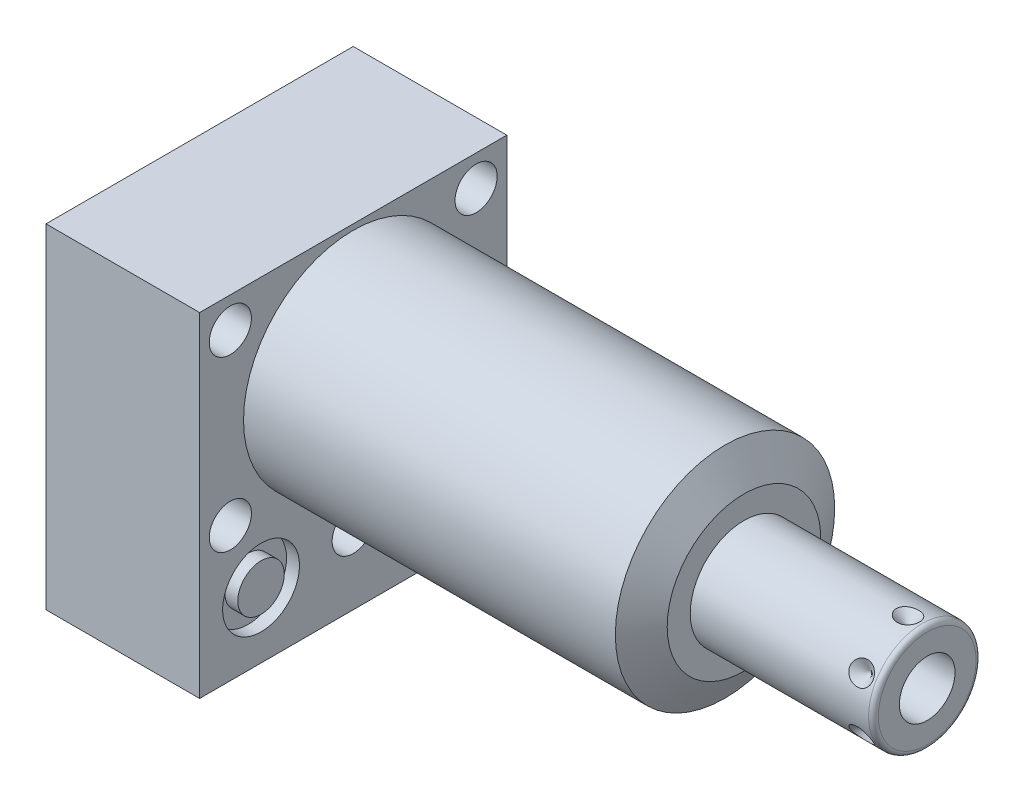
SolidWorks part; units mm, degrees
material "Alloy Steel"
ref_plane "Front Plane" through (0, 0, 0) normal (0, 0, 1) x (1, 0, 0)
ref_plane "Top Plane" through (0, 0, 0) normal (0, 1, 0) x (1, 0, 0)
ref_plane "Right Plane" through (0, 0, 0) normal (1, 0, 0) x (0, 0, -1)
ref_plane "Plane1" through (0, 0, 0) normal (1, 0, 0) x (0, 0, -1)
sketch "Sketch1" plane through (0, 0, 0) normal (1, 0, 0) x (0, 0, -1)
  line L0 (-31.75, 23.8252) -> (-31.75, -45.2628)
  line L1 (-31.75, -45.2628) -> (31.75, -45.2628)
  line L2 (31.75, -45.2628) -> (31.75, 23.8252)
  line L3 (31.75, 23.8252) -> (-31.75, 23.8252)
  line L4 (0, -55.6514) -> (0, 27.6098) construction
  dimension "D1" = 63.5
  dimension "D2" = 69.088
  dimension "D3" = 23.8252
extrude "Extrude1" add sketch "Sketch1" along normal blind 80.772 and the other way blind 31.75
ref_plane "Plane2" through (0, 0, 0) normal (1, 0, 0) x (0, 0, -1)
sketch "Sketch2" plane through (0, 0, 0) normal (1, 0, 0) x (0, 0, -1)
  line L0 (-26.0541, 0) -> (26.0541, 0) construction
  line L5 (31.75, 23.8252) -> (-31.75, 23.8252)
  line L6 (-31.75, 23.8252) -> (-31.75, -45.2628)
  line L7 (-31.75, -45.2628) -> (31.75, -45.2628)
  line L8 (31.75, -45.2628) -> (31.75, 23.8252)
  line L9 (31.75, 23.8252) -> (-31.75, 23.8252)
  line L10 (-31.75, 23.8252) -> (-31.75, -45.2628)
  line L11 (-31.75, -45.2628) -> (31.75, -45.2628)
  line L12 (31.75, -45.2628) -> (31.75, 23.8252)
  circle A0 centre (0, 0) radius 22.6695
  dimension "D1" = 45.339
  dimension "D2" = 0
extrude "Cut-Extrude1" cut sketch "Sketch2" along normal up to next
ref_plane "Plane3" through (0, 0, 0) normal (0, 0, 1) x (1, 0, 0)
sketch "Sketch3" plane through (0, 0, 0) normal (0, 0, 1) x (1, 0, 0)
  line L0 (76.8492, 22.6695) -> (80.772, 15.875)
  line L1 (76.0371, 0) -> (80.9975, 0) construction
  line L2 (80.772, 22.6695) -> (80.772, 15.875)
  line L3 (80.772, 22.6695) -> (76.8492, 22.6695)
  line L4 (80.772, 22.6695) -> (0, 22.6695) construction
  line L5 (80.772, -22.6695) -> (80.772, 22.6695) construction
  dimension "D1" = 31.75
  dimension "D2" = 30
revolve "Cut-Revolve1" cut sketch "Sketch3" angle 360 about L1
ref_plane "Plane4" through (-29.083, -31.75, 19.05) normal (0, 0, 1) x (0, 1, 0)
sketch "S2D0002" plane through (-29.083, -31.75, 19.05) normal (0, 0, 1) x (0, 1, 0)
  line L0 (0, 0) -> (4.5466, 0)
  line L1 (4.5466, 0) -> (4.1066, -2.0701)
  line L2 (4.1066, -2.0701) -> (3.4544, -2.7223)
  line L3 (3.4544, -2.7223) -> (3.4544, -13.97)
  line L4 (3.4544, -13.97) -> (0, -13.97)
  line L5 (0, -13.97) -> (0, 0)
  line L6 (0, -14.6685) -> (0, 0.6985) construction
  dimension "D1" = 13.97
revolve "Cut-Revolve2" cut sketch "S2D0002" angle 360 about L6
ref_plane "Plane5" through (-29.083, -31.75, -19.05) normal (0, 0, 1) x (0, 1, 0)
sketch "Sketch5" plane through (-29.083, -31.75, -19.05) normal (0, 0, 1) x (0, 1, 0)
  line L0 (0, 0) -> (4.5466, 0)
  line L1 (4.5466, 0) -> (4.1066, -2.0701)
  line L2 (4.1066, -2.0701) -> (3.4544, -2.7223)
  line L3 (3.4544, -2.7223) -> (3.4544, -13.97)
  line L4 (3.4544, -13.97) -> (0, -13.97)
  line L5 (0, -13.97) -> (0, 0)
  line L6 (0, -14.6685) -> (0, 0.6985) construction
  dimension "D1" = 13.97
revolve "Cut-Revolve3" cut sketch "Sketch5" angle 360 about L6
ref_plane "Plane6" through (-2.667, -31.75, 19.05) normal (0, 0, 1) x (0, -1, 0)
sketch "Sketch6" plane through (-2.667, -31.75, 19.05) normal (0, 0, 1) x (0, -1, 0)
  line L0 (0, 0) -> (4.5466, 0)
  line L1 (4.5466, 0) -> (4.1066, -2.0701)
  line L2 (4.1066, -2.0701) -> (3.4544, -2.7223)
  line L3 (3.4544, -2.7223) -> (3.4544, -12.192)
  line L4 (3.4544, -12.192) -> (0, -12.192)
  line L5 (0, -12.192) -> (0, 0)
  line L6 (0, -12.8016) -> (0, 0.6096) construction
  dimension "D1" = 12.192
revolve "Cut-Revolve4" cut sketch "Sketch6" angle 360 about L6
ref_plane "Plane7" through (-2.667, -31.75, -19.05) normal (0, 0, 1) x (0, -1, 0)
sketch "Sketch7" plane through (-2.667, -31.75, -19.05) normal (0, 0, 1) x (0, -1, 0)
  line L0 (0, 0) -> (4.5466, 0)
  line L1 (4.5466, 0) -> (4.1066, -2.0701)
  line L2 (4.1066, -2.0701) -> (3.4544, -2.7223)
  line L3 (3.4544, -2.7223) -> (3.4544, -12.192)
  line L4 (3.4544, -12.192) -> (0, -12.192)
  line L5 (0, -12.192) -> (0, 0)
  line L6 (0, -12.8016) -> (0, 0.6096) construction
  dimension "D1" = 12.192
revolve "Cut-Revolve5" cut sketch "Sketch7" angle 360 about L6
ref_plane "Plane8" through (-15.875, -51.6128, 19.05) normal (0, 0, 1) x (-1, 0, 0)
sketch "Sketch8" plane through (-15.875, -51.6128, 19.05) normal (0, 0, 1) x (-1, 0, 0)
  line L0 (0, -6.604) -> (6.1849, -6.604)
  line L1 (6.1849, -6.604) -> (5.6423, -9.1567)
  line L2 (5.6423, -9.1567) -> (4.9784, -9.8206)
  line L3 (4.9784, -9.8206) -> (4.9784, -25.654)
  line L4 (4.9784, -25.654) -> (0, -25.654)
  line L5 (0, -25.654) -> (0, -6.604)
  line L6 (0, -26.67) -> (0, 1.27) construction
  line L8 (15.875, -6.35) -> (-15.875, -6.35) construction
  dimension "D1" = 19.05
  dimension "D2" = 0.254
revolve "Cut-Revolve6" cut sketch "Sketch8" angle 360 about L6
ref_plane "Plane9" through (-15.875, -51.6128, -19.05) normal (0, 0, 1) x (-1, 0, 0)
sketch "Sketch9" plane through (-15.875, -51.6128, -19.05) normal (0, 0, 1) x (-1, 0, 0)
  line L0 (0, -6.604) -> (6.1849, -6.604)
  line L1 (6.1849, -6.604) -> (5.6423, -9.1567)
  line L2 (5.6423, -9.1567) -> (4.9784, -9.8206)
  line L3 (4.9784, -9.8206) -> (4.9784, -25.654)
  line L4 (4.9784, -25.654) -> (0, -25.654)
  line L5 (0, -25.654) -> (0, -6.604)
  line L6 (0, -26.67) -> (0, 1.27) construction
  line L7 (15.875, -6.35) -> (-15.875, -6.35) construction
  dimension "D1" = 19.05
  dimension "D2" = 0.254
revolve "Cut-Revolve7" cut sketch "Sketch9" angle 360 about L6
ref_plane "Plane10" through (0, 0, 0) normal (0, 0, 1) x (1, 0, 0)
sketch "Sketch18" plane through (0, 0, 0) normal (1, 0, 0) x (0, 0, -1)
  circle A0 centre (-19.05, -31.75) radius 7.9375
  circle A1 centre (19.05, -31.75) radius 7.9375
  dimension "D1" = 15.875
extrude "Cut-Extrude2" cut sketch "Sketch18" against normal blind 2.667
sketch "Sketch19" plane through (-31.75, 0, 0) normal (-1, 0, 0) x (0, 0, 1)
  circle A0 centre (-19.05, -31.75) radius 7.9375
  circle A1 centre (19.05, -31.75) radius 7.9375
  dimension "D1" = 15.875
extrude "Cut-Extrude3" cut sketch "Sketch19" against normal blind 2.667
sketch "Sketch20" plane through (0, -45.2628, 0) normal (0, -1, 0) x (1, 0, 0)
  circle A0 centre (-15.875, -19.05) radius 9.525
  circle A1 centre (-15.875, 19.05) radius 9.525
  circle A2 centre (-15.875, 19.05) radius 6.1849 construction
  dimension "D1" = 19.05
extrude "Cut-Extrude4" cut sketch "Sketch20" against normal blind 0.254
sketch "Sketch10" plane through (0, 0, 0) normal (0, 0, 1) x (1, 0, 0)
  line L0 (80.772, 0) -> (80.772, 11.1125)
  line L1 (80.772, 11.1125) -> (117.6274, 11.1125)
  line L2 (118.6434, 10.0965) -> (118.6434, 0)
  line L3 (118.6434, 0) -> (80.772, 0)
  line L4 (58.2708, 0) -> (120.537, 0) construction
  line L5 (80.772, -15.875) -> (80.772, 15.875) construction
  line L6 (-31.75, 23.8252) -> (-31.75, -45.2628) construction
  arc A0 (118.6434, 10.0965) -> (117.6274, 11.1125) centre (117.6274, 10.0965) ccw
  point P0 (80.772, 0)
  dimension "D2" = 1.016
  dimension "D1" = 22.225
  dimension "D3" = 150.3934
revolve "Revolve1" add sketch "Sketch10" angle 360 about L4
ref_plane "Plane11" through (118.6434, -5.7531, 0) normal (0, 0, 1) x (0, -1, 0)
sketch "S2D0001" plane through (118.6434, -5.7531, 0) normal (0, 0, 1) x (0, -1, 0)
  line L0 (0, 0) -> (0, -17.018)
  line L1 (0, -17.018) -> (-5.7531, -20.4748)
  line L2 (0, 0) -> (-5.7531, 0)
  line L3 (-5.7531, 0) -> (-5.7531, -20.4748)
  line L4 (-5.7531, -34.3471) -> (-5.7531, 1.0237) construction
  line L5 (4.3434, 0) -> (-15.8496, 0) construction
  dimension "D1" = 11.5062
  dimension "D2" = 17.018
  dimension "D3" = 59
revolve "Cut-Revolve8" cut sketch "S2D0001" angle 360 about L4
ref_plane "Plane12" through (-31.75, -51.6128, 0) normal (0, -1, 0) x (0, 0, -1)
sketch "Sketch12" plane through (0, -45.0088, 0) normal (0, -1, 0) x (1, 0, 0)
  circle A0 centre (-15.875, 19.05) radius 6.4389
  circle A1 centre (-15.875, 19.05) radius 9.525 construction
  dimension "D1" = 12.8778
extrude "Extrude2" add sketch "Sketch12" along normal blind 1.651
sketch "Sketch13" plane through (0, 0, 0) normal (1, 0, 0) x (0, 0, -1)
  circle A0 centre (-19.05, -31.75) radius 4.8006
  circle A1 centre (-19.05, -31.75) radius 7.9375 construction
  dimension "D1" = 9.6012
ref_plane "Plane13" through (-31.75, 0, 0) normal (1, 0, 0) x (0, 0, -1)
extrude "Extrude3" add sketch "Sketch13" along normal up to surface
ref_plane "Plane14" through (0, -31.75, -19.05) normal (0, -1, 0) x (0, 0, -1)
sketch "Sketch14" plane through (0, -31.75, -19.05) normal (0, -1, 0) x (0, 0, -1)
  line L0 (0, -2.8435) -> (0, 1.0401) construction
  line L1 (0, -5.3893) -> (0, -12.2901) construction
  line L2 (7.9375, -2.667) -> (-7.9375, -2.667) construction
  circle A0 centre (6.1722, -0.9017) radius 1.7653
  dimension "D1" = 3.5306
  dimension "D2" = 12.3444
revolve "Revolve2" add sketch "Sketch14" angle 360 about L0
ref_plane "Plane15" through (0, -31.75, -19.05) normal (0, -1, 0) x (0, 0, -1)
sketch "Sketch15" plane through (0, -31.75, -19.05) normal (0, -1, 0) x (0, 0, -1)
  line L0 (0, -32.7901) -> (0, -28.9065) construction
  line L1 (0, -29.083) -> (0, -27.0129) construction
  line L2 (-7.9375, -29.083) -> (7.9375, -29.083) construction
  circle A0 centre (6.1722, -30.8483) radius 1.7653
  dimension "D1" = 3.5306
  dimension "D2" = 12.3444
revolve "Revolve3" add sketch "Sketch15" angle 360 about L0
ref_plane "Plane16" through (114.681, -11.1125, 0) normal (0, 0, 1) x (-1, 0, 0)
sketch "Sketch16" plane through (114.681, -11.1125, 0) normal (0, 0, 1) x (-1, 0, 0)
  line L0 (0, 0) -> (2.413, 0)
  line L1 (2.413, 0) -> (0, -2.413)
  line L2 (0, 0) -> (0, -2.413)
  line L3 (0, -5.0193) -> (0, 0.1207) construction
  line L4 (33.909, 0) -> (-2.9464, 0) construction
  line L5 (-3.9624, -1.016) -> (-3.9624, -21.209) construction
  dimension "D1" = 3.9624
  dimension "D2" = 4.826
  dimension "D3" = 45
ref_plane "Plane17" through (114.681, 11.1125, 0) normal (0, 0, 1) x (1, 0, 0)
revolve "Cut-Revolve9" cut sketch "Sketch16" angle 360 about L3
pattern_circular "CirPattern1" count 6 over 360 of "Cut-Revolve9"
hole_wizard "Hole1" positions "Sketch22" profile "Sketch21" legacy end condition up to next
sketch "Sketch22" plane through (0, 0, 0) normal (1, 0, 0) x (0, 0, -1)
  line L0 (0, 0) -> (-38.8053, 0) construction
  line L1 (0, 0) -> (0, 31.2017) construction
  point P0 (-25.4, 17.4752)
  point P1 (0, -30.8356)
  point P12 (-25.4, -17.4752)
  point P14 (25.4, 17.4752)
  point P15 (25.4, -17.4752)
  dimension "D1" = 25.4
  dimension "D2" = 17.4752
  dimension "D3" = 30.8356
sketch "Sketch21" plane through (0, 17.4752, 25.4) normal (0, 1, 0) x (0, 0, -1)
  line L0 (0, 0) -> (0, 31.75)
  line L1 (0, 31.75) -> (4.3561, 31.75)
  line L2 (4.3561, 31.75) -> (4.3561, 0)
  line L3 (4.3561, 0) -> (0, 0)
  line L4 (0, 110) -> (0, -10) construction
  dimension "Diameter" = 8.7122
  dimension "Depth" = 31.75
